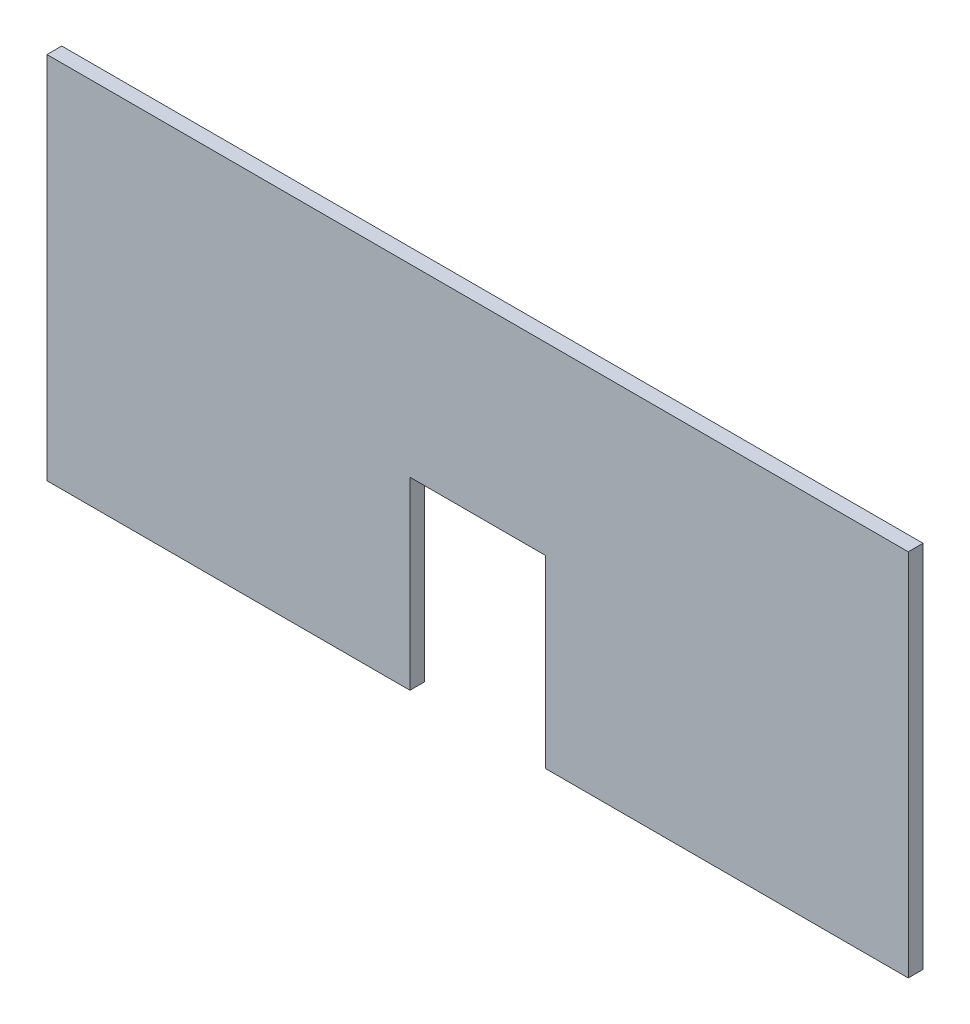
SolidWorks part; units mm, degrees
material "Plain Carbon Steel"
ref_plane "Front Plane" through (0, 0, 0) normal (0, 0, 1) x (1, 0, 0)
ref_plane "Top Plane" through (0, 0, 0) normal (0, 1, 0) x (1, 0, 0)
ref_plane "Right Plane" through (0, 0, 0) normal (1, 0, 0) x (0, 0, -1)
sketch "Sketch1" plane through (0, 0, 0) normal (0, 0, 1) x (1, 0, 0)
  line L0 (405, 0) -> (700, 0)
  line L1 (295, 150) -> (405, 150)
  line L2 (295, 150) -> (295, 0)
  line L4 (405, 150) -> (405, 0)
  line L5 (0, 300) -> (700, 300)
  line L6 (0, 300) -> (0, 0)
  line L7 (0, 0) -> (295, 0)
  line L8 (700, 300) -> (700, 0)
  dimension "D1" = 700
  dimension "D2" = 300
  dimension "D3" = 110
  dimension "D4" = 150
  dimension "D5" = 295
extrude "Boss-Extrude1" add sketch "Sketch1" along normal blind 12
